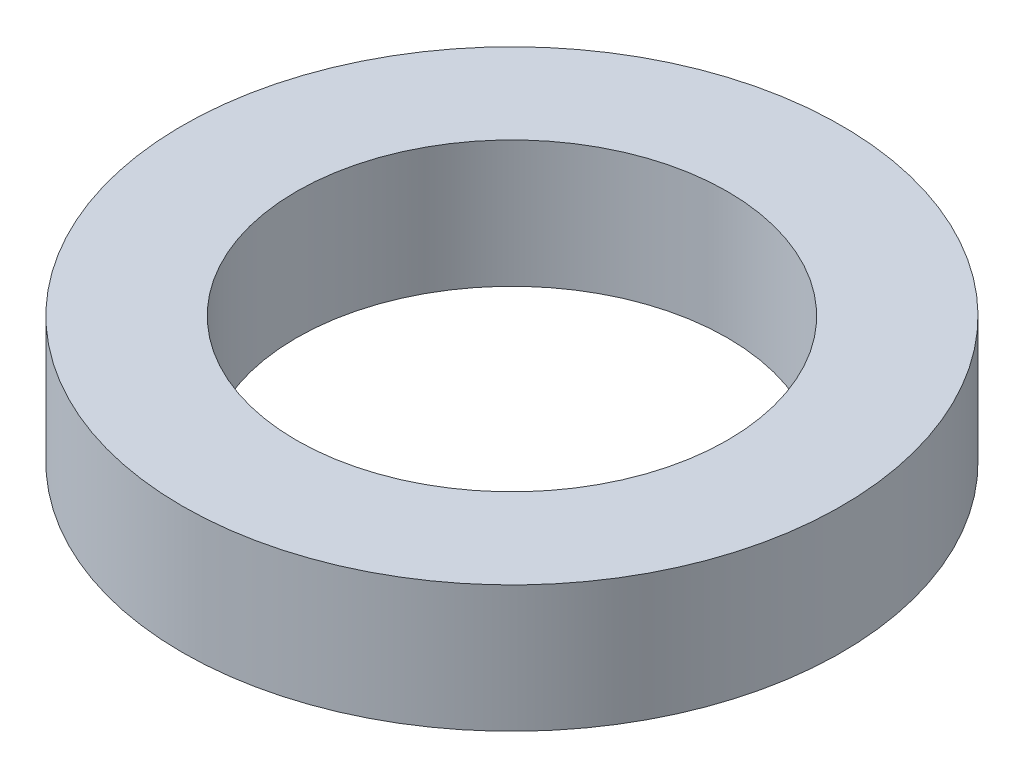
SolidWorks part; units mm, degrees
ref_plane "Front Plane" through (0, 0, 0) normal (0, 0, 1) x (1, 0, 0)
ref_plane "Top Plane" through (0, 0, 0) normal (0, 1, 0) x (1, 0, 0)
ref_plane "Right Plane" through (0, 0, 0) normal (1, 0, 0) x (0, 0, -1)
sketch "Sketch1" plane through (0, 0, 0) normal (0, 1, 0) x (1, 0, 0)
  circle A0 centre (0, 0) radius 13
  circle A1 centre (0, 0) radius 8.5
  dimension "D1" = 17
  dimension "D2" = 26
extrude "Boss-Extrude1" add sketch "Sketch1" along normal blind 5
